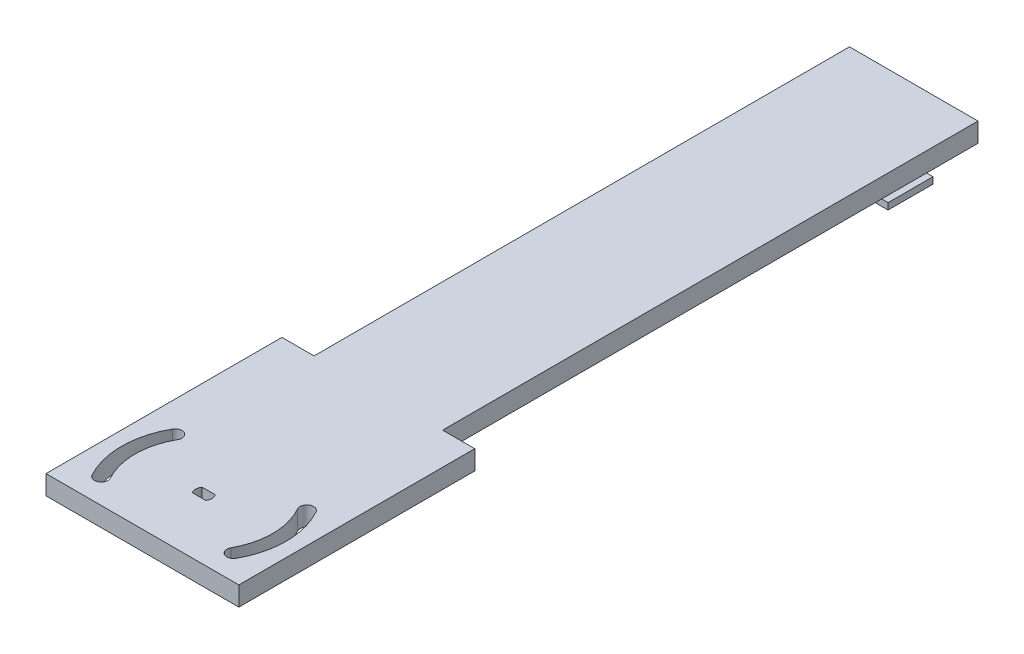
SolidWorks part; units mm, degrees
ref_plane "Front Plane" through (0, 0, 0) normal (0, 0, 1) x (1, 0, 0)
ref_plane "Top Plane" through (0, 0, 0) normal (0, 1, 0) x (1, 0, 0)
ref_plane "Right Plane" through (0, 0, 0) normal (1, 0, 0) x (0, 0, -1)
sketch "Sketch1" plane through (0, 0, 0) normal (0, 1, 0) x (1, 0, 0)
  line L1 (-20, -120) -> (20, -120)
  line L2 (-20, -120) -> (-20, 120)
  line L3 (-20, 120) -> (20, 120)
  line L4 (20, -120) -> (20, 120)
  line L5 (-20, -120) -> (20, 120) construction
  line L6 (-20, 120) -> (20, -120) construction
  point P0 (0, 0)
  dimension "D1" = 40
  dimension "D2" = 240
extrude "Boss-Extrude1" add sketch "Sketch1" along normal blind 6
sketch "Sketch3" plane through (20, 0, 0) normal (1, 0, 0) x (0, 0, -1)
  line L0 (-120, 0) -> (120, 0) construction
  line L1 (-120, 6) -> (-46.5869, 6)
  line L2 (-120, 6) -> (-120, 0)
  line L3 (-120, 0) -> (-46.5869, 0)
  line L4 (-46.5869, 6) -> (-46.5869, 0)
extrude "Boss-Extrude2" add sketch "Sketch3" along normal blind 10 and the other way blind 50
sketch "Sketch2" plane through (0, 0, 0) normal (0, -1, 0) x (1, 0, 0)
  line L6 (-2.05, 99.3744) -> (2.05, 99.3744)
  line L9 (-2.05, 102.3744) -> (2.05, 102.3744)
  arc A16 (-2.05, 102.3744) -> (-2.05, 99.3744) centre (0, 100.8744) ccw
  arc A17 (2.05, 99.3744) -> (2.05, 102.3744) centre (0, 100.8744) ccw
  arc A18 (-21.42, 100.8744) -> (-18.659, 90.355) centre (0, 100.8744) ccw
  arc A19 (-25.62, 100.8744) -> (-22.3177, 88.2924) centre (0, 100.8744) ccw
  arc A20 (-21.42, 100.8744) -> (-18.7685, 111.1971) centre (0, 100.8744) cw
  arc A21 (-25.62, 100.8744) -> (-22.4487, 113.2211) centre (0, 100.8744) cw
  arc A22 (-22.4487, 113.2211) -> (-18.7685, 111.1971) centre (-20.6086, 112.2091) cw
  arc A23 (-18.659, 90.355) -> (-22.3177, 88.2924) centre (-20.4883, 89.3237) cw
  arc A24 (25.62, 100.8744) -> (22.3177, 88.2924) centre (0, 100.8744) cw
  arc A25 (25.62, 100.8744) -> (22.4487, 113.2211) centre (0, 100.8744) ccw
  arc A26 (22.4487, 113.2211) -> (18.7685, 111.1971) centre (20.6086, 112.2091) ccw
  arc A27 (21.42, 100.8744) -> (18.7685, 111.1971) centre (0, 100.8744) ccw
  arc A28 (21.42, 100.8744) -> (18.659, 90.355) centre (0, 100.8744) cw
  arc A29 (18.659, 90.355) -> (22.3177, 88.2924) centre (20.4883, 89.3237) ccw
  point P2 (0, 100.8744)
  point P23 (0, 0)
  dimension "D1" = 4.1
  dimension "D2" = 4.1
  dimension "D3" = 3
  dimension "D4" = 3
sketch "Sketch4" plane through (0, 0, 0) normal (0, -1, 0) x (1, 0, 0)
  line L0 (-14, -110) -> (14, -110)
  line L1 (-14, -110) -> (-14, -96)
  line L2 (-14, -96) -> (14, -96)
  line L3 (14, -110) -> (14, -96)
  line L4 (20, -120) -> (-20, -120) construction
  point P4 (0, -96)
  dimension "D1" = 14
  dimension "D2" = 28
  dimension "D3" = 10
extrude "Boss-Extrude3" add sketch "Sketch4" along normal blind 8
sketch "Sketch5" plane through (14, 0, 0) normal (1, 0, 0) x (0, 0, -1)
  line L0 (96, -8) -> (110, -8)
  line L1 (96, -8) -> (96, -6)
  line L2 (96, -6) -> (110, -6)
  line L3 (110, -8) -> (110, -6)
  line L4 (96, -8) -> (96, 0) construction
  line L5 (110, -8) -> (96, -8) construction
  line L6 (110, -8) -> (110, 0) construction
  dimension "D1" = 2
extrude "Boss-Extrude4" add sketch "Sketch5" along normal blind 2 and the other way blind 30
extrude "Cut-Extrude1" cut sketch "Sketch2" against normal blind 10
